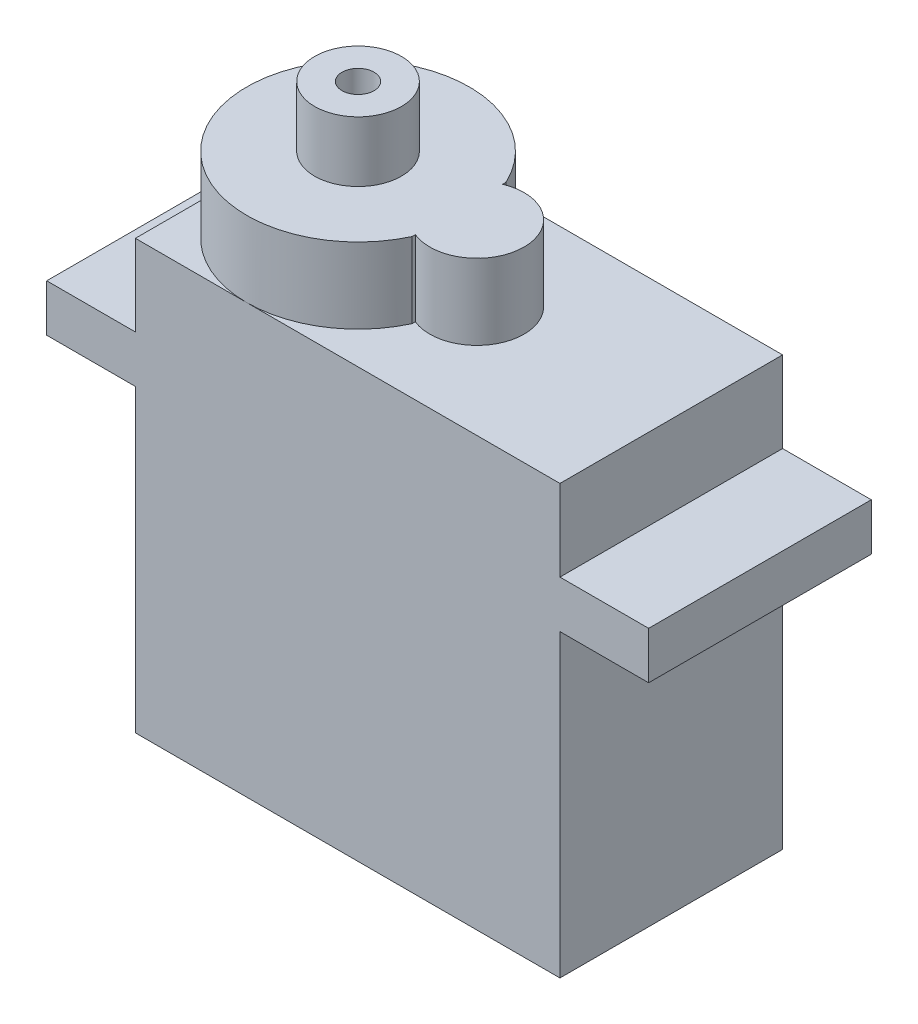
SolidWorks part; units mm, degrees
ref_plane "Alzado" through (0, 0, 0) normal (0, 0, 1) x (1, 0, 0)
ref_plane "Planta" through (0, 0, 0) normal (0, 1, 0) x (1, 0, 0)
ref_plane "Vista lateral" through (0, 0, 0) normal (1, 0, 0) x (0, 0, -1)
sketch "Croquis1" plane through (0, 0, 0) normal (0, 0, 1) x (1, 0, 0)
  line L0 (-11.25, 4.55) -> (11.25, 4.55)
  line L1 (-11.25, -11.35) -> (11.25, -11.35)
  line L2 (-11.25, -11.35) -> (-11.25, 11.35)
  line L3 (-11.25, 11.35) -> (11.25, 11.35)
  line L4 (11.25, -11.35) -> (11.25, 11.35)
  line L5 (-11.25, -11.35) -> (11.25, 11.35) construction
  line L6 (-11.25, 11.35) -> (11.25, -11.35) construction
  line L7 (11.25, 4.55) -> (15.95, 4.55)
  line L8 (15.95, 4.55) -> (15.95, 7.05)
  line L9 (15.95, 7.05) -> (11.25, 7.05)
  line L10 (-11.25, 4.55) -> (-15.95, 4.55)
  line L11 (-15.95, 4.55) -> (-15.95, 7.05)
  line L12 (-15.95, 7.05) -> (-11.25, 7.05)
  point P0 (0, 0)
  dimension "D1" = 22.5
  dimension "D2" = 22.7
  dimension "D3" = 15.9
  dimension "D4" = 2.5
  dimension "D5" = 4.7
  dimension "D6" = 4.7
  dimension "D7" = 2.5
extrude "Saliente-Extruir1" add sketch "Croquis1" along normal blind 11.8 contours L12 L11 L10 L2 | L0 L4 L3 L2 | L1 L4 L0 L2 | L8 L9 L4 L7
sketch "Croquis3" plane through (0, 11.35, 0) normal (0, 1, 0) x (1, 0, 0)
  line L0 (-15.95, -5.9) -> (15.95, -5.9)
  line L1 (-15.95, -11.8) -> (-15.95, 0) construction
  line L2 (15.95, -11.8) -> (15.95, 0) construction
  line L3 (0, 0) -> (0, -11.8)
  line L4 (-11.25, -11.8) -> (11.25, -11.8) construction
  line L5 (-11.25, -11.8) -> (-11.25, 0) construction
  line L6 (-11.25, -11.8) -> (-11.25, 0) construction
  circle A0 centre (-5.35, -5.9) radius 5.9
  circle A1 centre (0.95, -5.9) radius 2.5
  dimension "D1" = 5.9
  dimension "D2" = 5
  dimension "D3" = 12.2
extrude "Saliente-Extruir2" add sketch "Croquis3" along normal blind 4 contours L0 A1 A0 | A0 A1 L0 | L3 A1 L0 | L0 A1 L3 | A0 A1 L3 L0 | L3 A1 A0 L0 | A1 L3 A0 L0 | A1 L0 A0 L3
sketch "Croquis4" plane through (0, 15.35, 0) normal (0, 1, 0) x (1, 0, 0)
  line L0 (-11.25, -5.9) -> (15.95, -5.9)
  line L1 (-11.25, -11.8) -> (-11.25, 0) construction
  line L2 (15.95, -11.8) -> (15.95, 0) construction
  circle A0 centre (-5.35, -5.9) radius 2.3
  circle A1 centre (-5.35, -5.9) radius 0.85
  arc A2 (-5.35, 0) -> (-11.25, -5.9) centre (-5.35, -5.9) ccw construction
  dimension "D1" = 0
  dimension "D2" = 4.6
  dimension "D3" = 1.7
extrude "Saliente-Extruir3" add sketch "Croquis4" along normal blind 3.2 contours A1 L0 A0 | A1 L0 A0
